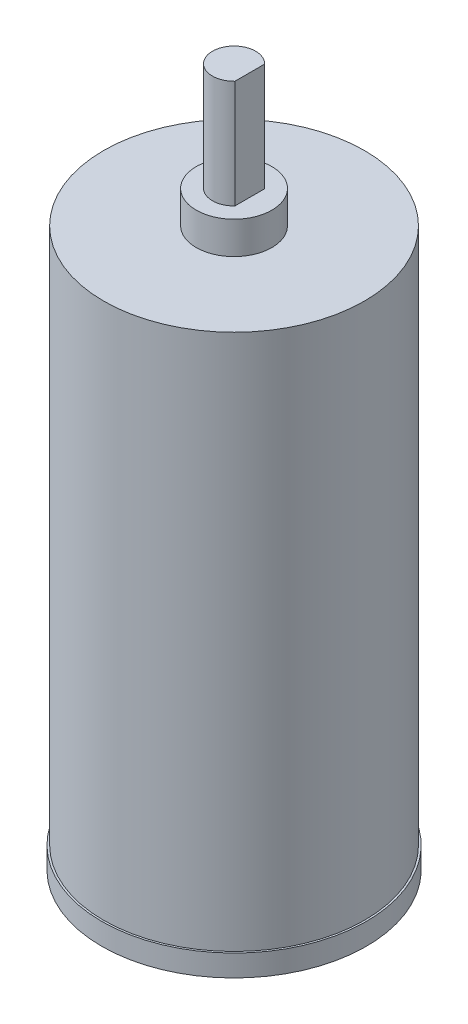
SolidWorks part; units mm, degrees
ref_plane "Спереди" through (0, 0, 0) normal (0, 0, 1) x (1, 0, 0)
ref_plane "Сверху" through (0, 0, 0) normal (0, 1, 0) x (1, 0, 0)
ref_plane "Справа" through (0, 0, 0) normal (1, 0, 0) x (0, 0, -1)
other "Configuration Table"
sketch "Эскиз1" plane through (0, 0, 0) normal (0, 1, 0) x (1, 0, 0)
  circle A0 centre (0, 0) radius 12.25
extrude "Бобышка-Вытянуть1" add sketch "Эскиз1" along normal blind 2
sketch "Эскиз2" plane through (0, 0, 0) normal (0, 1, 0) x (1, 0, 0)
  circle A0 centre (0, 0) radius 12.075
extrude "Бобышка-Вытянуть2" add sketch "Эскиз2" along normal blind 51.65
sketch "Эскиз3" plane through (0, 51.65, 0) normal (0, 1, 0) x (1, 0, 0)
  circle A0 centre (0, 0) radius 3.5
extrude "Бобышка-Вытянуть3" add sketch "Эскиз3" along normal blind 3
sketch "Эскиз4" plane through (0, 54.65, 0) normal (0, 1, 0) x (1, 0, 0)
  line L1 (1.45, 0) -> (1.45, 1.3775)
  line L2 (1.45, 0) -> (1.45, -1.3775)
  arc A0 (1.45, 1.3775) -> (1.45, -1.3775) centre (0, 0) ccw
extrude "Бобышка-Вытянуть4" add sketch "Эскиз4" along normal blind 10
